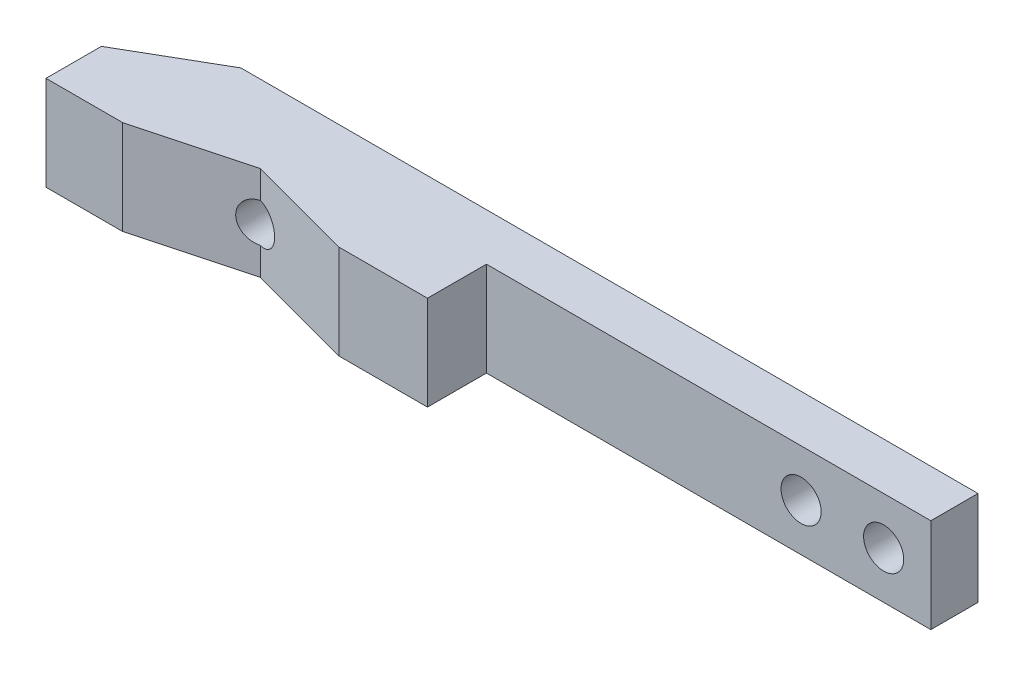
SolidWorks part; units mm, degrees
material "1.0037 (S235JR)"
ref_plane "Front Plane" through (0, 0, 0) normal (0, 0, 1) x (1, 0, 0)
ref_plane "Top Plane" through (0, 0, 0) normal (0, 1, 0) x (1, 0, 0)
ref_plane "Right Plane" through (0, 0, 0) normal (1, 0, 0) x (0, 0, -1)
sketch "Sketch1" plane through (0, 0, 0) normal (0, 1, 0) x (1, 0, 0)
  line L4 (35.397, 0.2122) -> (35.397, -3.7878)
  line L5 (-34.6011, 3.7026) -> (35.397, -3.7878) construction
  line L6 (-34.6029, -4.1177) -> (35.397, 4.2122) construction
  line L8 (-34.6029, -4.1177) -> (-34.6029, -8.8148)
  line L9 (-34.6029, -8.8148) -> (-28.1029, -8.8148)
  line L13 (-2.2832, -3.7878) -> (35.397, -3.7878)
  line L18 (-9.7832, -8.7878) -> (-2.2832, -8.7878)
  line L19 (-2.2832, -8.7878) -> (-2.2832, -3.7878)
  line L22 (-28.1029, -8.8148) -> (-18.8926, -6.3469)
  line L23 (-9.7832, -8.7878) -> (-18.8926, -6.3469)
  line L24 (35.397, 0.2122) -> (-27.1033, 0.2122)
  line L25 (-34.6029, -4.1177) -> (-27.1033, 0.2122)
  point P0 (0, 0)
  dimension "D1" = 8
  dimension "D2" = 70
  dimension "D3" = 7.5
  dimension "D4" = 18.3197
  dimension "D5" = 6.5
  dimension "D6" = 15
  dimension "D7" = 15
  dimension "D8" = 37.6803
  dimension "D9" = 60
extrude "Boss-Extrude2" add sketch "Sketch1" along normal blind 8
hole_wizard "M4 Tapped Hole1" positions "Sketch4" profile "Sketch5" tap size "M4" standard "DIN"
sketch "Sketch4" plane through (0, 0, -0.2122) normal (0, 0, -1) x (-1, 0, 0)
  line L1 (34.6029, 8) -> (34.6029, 0) construction
  point P0 (18.8929, 4)
  dimension "D1" = 15.71
sketch "Sketch5" plane through (-18.8929, 4, -0.2122) normal (1, 0, 0) x (0, 1, 0)
  line L0 (0, 0) -> (0, 12.4914)
  line L1 (0, 12.4914) -> (1.65, 11.5)
  line L2 (1.65, 11.5) -> (1.65, 0)
  line L5 (1.65, 0) -> (0, 0)
  line L10 (0, 12.4914) -> (-1.65, 11.5) construction
  line L11 (0, -6.35) -> (0, 107.95) construction
  dimension "Tap Drill Dia." = 3.3
  dimension "Tap Drill Depth" = 11.5
  dimension "Drill Angle" = 118
cosmetic thread "Hole Thread3" parameters "D1"=8, "D2"=4
sketch "Sketch8" plane through (0, 0, -0.2122) normal (0, 0, -1) x (-1, 0, 0)
  line L0 (-35.397, 8) -> (-35.397, 0) construction
  circle A0 centre (-31.397, 4) radius 1.7
  circle A1 centre (-24.397, 4) radius 1.7
  dimension "D3" = 3.4
  dimension "D4" = 3.4
  dimension "D1" = 4
  dimension "D2" = 7
extrude "Cut-Extrude1" cut sketch "Sketch8" against normal blind 10
